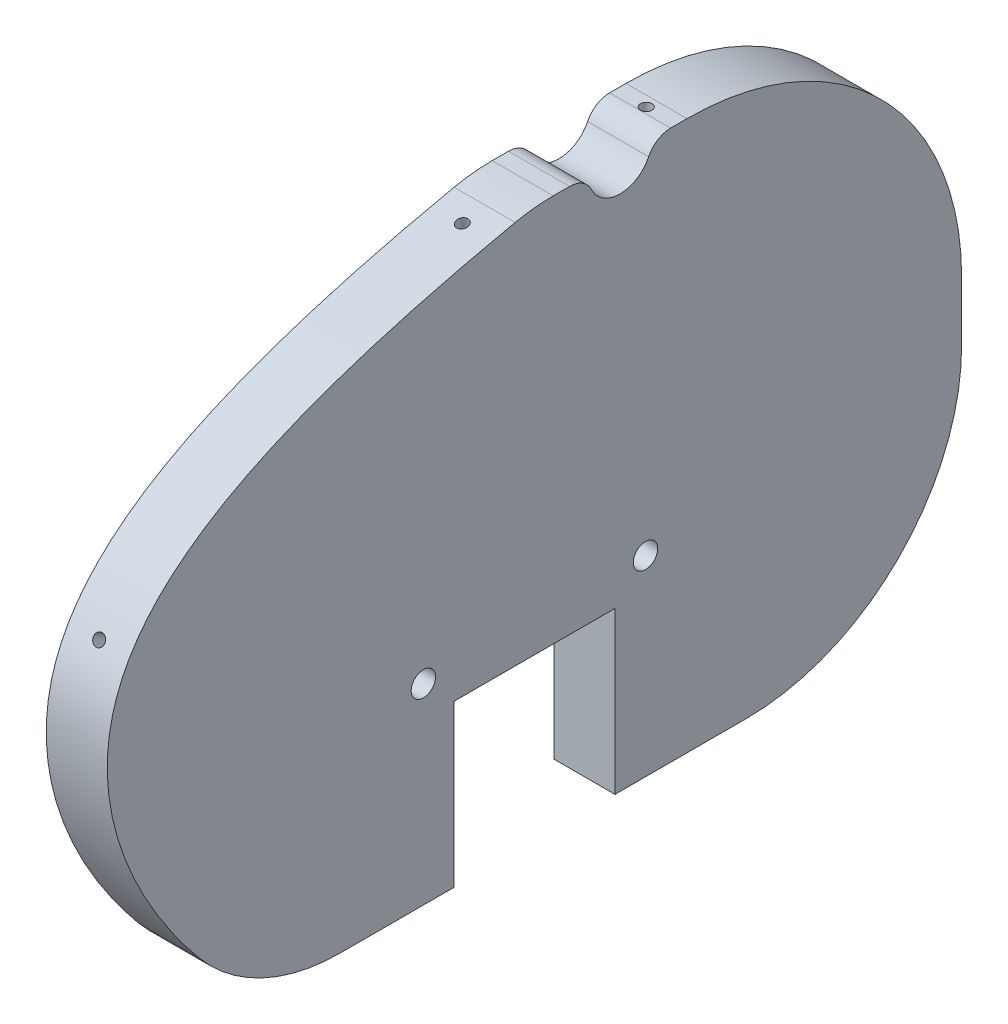
SolidWorks part; units mm, degrees
material "Oak"
ref_plane "Front Plane" through (0, 0, 0) normal (0, 0, 1) x (1, 0, 0)
ref_plane "Top Plane" through (0, 0, 0) normal (0, 1, 0) x (1, 0, 0)
ref_plane "Right Plane" through (0, 0, 0) normal (1, 0, 0) x (0, 0, -1)
sketch "Sketch1" plane through (0, 0, 0) normal (1, 0, 0) x (0, 0, -1)
  line L0 (0, 28.575) -> (0, -11.811) construction
  line L1 (1.949, 28.575) -> (15.875, 28.575)
  line L2 (-44.45, 0) -> (-44.45, -1.025)
  line L3 (-20.2212, -28.575) -> (-8.382, -28.575)
  line L4 (44.45, 0) -> (44.45, -6.1908)
  line L5 (-44.45, 28.575) -> (44.45, -28.575) construction
  line L6 (-44.45, -28.575) -> (44.45, 28.575) construction
  line L7 (-8.382, -11.811) -> (8.382, -11.811)
  line L8 (-8.382, -11.811) -> (-8.382, -28.575)
  line L9 (-44.45, 0) -> (0, 0) construction
  line L10 (8.382, -11.811) -> (8.382, -28.575)
  line L11 (-8.382, -11.811) -> (8.382, -28.575) construction
  line L12 (-8.382, -28.575) -> (8.382, -11.811) construction
  line L13 (8.382, -28.575) -> (22.0658, -28.575)
  line L14 (0, 0) -> (44.45, 0) construction
  arc A2 (22.0658, -28.575) -> (44.45, -6.1908) centre (22.0658, -6.1908) ccw
  arc A3 (44.45, 0) -> (15.875, 28.575) centre (15.875, 0) ccw
  arc A4 (-2.0065, 28.1598) -> (1.949, 28.575) centre (1.949, 9.525) cw
  arc A5 (-34.9185, -21.6448) -> (-20.2212, -28.575) centre (-20.2212, -9.525) ccw
  spline S0 degree 3 poles (-2.0065, 28.1598) (-30.4961, 22.1125) (-51.1965, 9.9804) (-41.1933, -14.0356) (-34.9185, -21.6448) knots 0.014283 0.014283 0.014283 0.014283 0.629768 0.915552 0.915552 0.915552 0.915552
  point P0 (0, 0)
  point P6 (0, -20.193)
  dimension "D5" = 19.05
  dimension "D6" = 19.05
  dimension "D1" = 88.9
  dimension "D2" = 57.15
  dimension "D3" = 16.764
  dimension "D4" = 16.764
extrude "Boss-Extrude1" add sketch "Sketch1" along normal mid plane 6.35 contours A4 S0 A5 L3 L8 L7 L10 L13 A2 L4 A3 L1
sketch "Sketch2" plane through (3.175, 0, 0) normal (1, 0, 0) x (0, 0, -1)
  line L0 (1.949, 28.575) -> (15.875, 28.575) construction
  circle A0 centre (8.912, 28.575) radius 3.302
  dimension "D1" = 6.604
extrude "Cut-Extrude1" cut sketch "Sketch2" against normal through all
fillet "Fillet1" radius 2.54 2 edges at (0, 28.575, -5.61) (0, 28.575, -12.214)
sketch "Sketch3" plane through (3.175, 0, 0) normal (1, 0, 0) x (0, 0, -1)
  line L0 (-8.382, -11.811) -> (8.382, -11.811) construction
  line L1 (8.382, -11.811) -> (8.382, -28.575) construction
  line L2 (-8.382, -11.811) -> (-8.382, -28.575) construction
  circle A0 centre (11.557, -8.636) radius 1.27
  circle A1 centre (-11.557, -8.636) radius 1.27
  dimension "D1" = 2.54
  dimension "D2" = 3.175
  dimension "D3" = 3.175
  dimension "D4" = 3.175
  dimension "D5" = 3.175
extrude "Cut-Extrude2" cut sketch "Sketch3" against normal through all
hole_wizard "3/64 (0.04688) Diameter Hole4" positions "3DSketch4" profile "Sketch7" hole size "3/64" standard "ANSI Inch"
sketch3d "3DSketch4"
  line L0 (3.175, 28.575, -1.949) -> (-3.175, 28.575, -1.949) construction
  point P0 (0, 27.6537, 4.3338)
  dimension "D1" = 6.35
sketch "Sketch7" plane through (0, 27.6537, 4.3338) normal (1, 0, 0) x (0, -0.2176, 0.976)
  line L0 (0, 0) -> (0, 6.7077)
  line L1 (0, 6.7077) -> (0.5954, 6.35)
  line L2 (0.5954, 6.35) -> (0.5954, 0)
  line L5 (0.5954, 0) -> (0, 0)
  line L10 (0, 6.7077) -> (-0.5954, 6.35) construction
  line L11 (0, -6.35) -> (0, 107.95) construction
  dimension "Hole Dia." = 1.1908
  dimension "Hole Depth" = 6.35
  dimension "Drill Angle" = 118
hole_wizard "3/64 (0.04688) Diameter Hole5" positions "Sketch9" profile "Sketch8" hole size "3/64" standard "ANSI Inch"
sketch "Sketch9" plane through (0, 28.575, 0) normal (0, 1, 0) x (1, 0, 0)
  line L0 (-3.175, 14.1729) -> (3.175, 14.1729) construction
  line L1 (0, -31.4325) -> (0, 31.4325) construction
  point P0 (0, 14.8079)
  dimension "D1" = 0.635
sketch "Sketch8" plane through (0, 28.575, -14.8079) normal (1, 0, 0) x (0, 0, 1)
  line L0 (0, 0) -> (0, 6.7077)
  line L1 (0, 6.7077) -> (0.5954, 6.35)
  line L2 (0.5954, 6.35) -> (0.5954, 0)
  line L5 (0.5954, 0) -> (0, 0)
  line L10 (0, 6.7077) -> (-0.5954, 6.35) construction
  line L11 (0, -6.35) -> (0, 107.95) construction
  dimension "Hole Dia." = 1.1908
  dimension "Hole Depth" = 6.35
  dimension "Drill Angle" = 118
hole_wizard "3/64 (0.04688) Diameter Hole8" positions "3DSketch7" profile "Sketch12" hole size "3/64" standard "ANSI Inch"
sketch3d "3DSketch7"
  line L0 (-3.175, -11.811, 8.382) -> (-3.175, -11.811, -8.382) construction
  point P0 (0, 6.9726, -43.5863)
  dimension "D1" = 19.05
sketch "Sketch12" plane through (0, 6.9726, -43.5863) normal (1, 0, 0) x (0, 0.9698, 0.244)
  line L0 (0, 0) -> (0, 6.7077)
  line L1 (0, 6.7077) -> (0.5954, 6.35)
  line L2 (0.5954, 6.35) -> (0.5954, 0)
  line L5 (0.5954, 0) -> (0, 0)
  line L10 (0, 6.7077) -> (-0.5954, 6.35) construction
  line L11 (0, -6.35) -> (0, 107.95) construction
  dimension "Hole Dia." = 1.1908
  dimension "Hole Depth" = 6.35
  dimension "Drill Angle" = 118
hole_wizard "3/64 (0.04688) Diameter Hole10" positions "3DSketch9" profile "Sketch14" hole size "3/64" standard "ANSI Inch"
sketch3d "3DSketch9"
  line L0 (3.175, -28.575, -22.0658) -> (-3.175, -28.575, -22.0658) construction
  point P0 (0, -20.4688, -39.305)
  dimension "D1" = 19.05
sketch "Sketch14" plane through (0, -20.4688, -39.305) normal (1, 0, 0) x (0, 0.7702, -0.6379)
  line L0 (0, 0) -> (0, 6.7077)
  line L1 (0, 6.7077) -> (0.5954, 6.35)
  line L2 (0.5954, 6.35) -> (0.5954, 0)
  line L5 (0.5954, 0) -> (0, 0)
  line L10 (0, 6.7077) -> (-0.5954, 6.35) construction
  line L11 (0, -6.35) -> (0, 107.95) construction
  dimension "Hole Dia." = 1.1908
  dimension "Hole Depth" = 6.35
  dimension "Drill Angle" = 118
hole_wizard "3/64 (0.04688) Diameter Hole11" positions "Sketch16" profile "Sketch15" hole size "3/64" standard "ANSI Inch"
sketch "Sketch16" plane through (0, -28.575, 0) normal (0, -1, 0) x (-1, 0, 0)
  line L0 (0, 31.4325) -> (0, -31.4325) construction
  line L1 (-3.175, 8.382) -> (3.175, 8.382) construction
  point P0 (0, 10.922)
  dimension "D1" = 2.54
sketch "Sketch15" plane through (0, -28.575, -10.922) normal (1, 0, 0) x (0, 0, -1)
  line L0 (0, 0) -> (0, 6.7077)
  line L1 (0, 6.7077) -> (0.5954, 6.35)
  line L2 (0.5954, 6.35) -> (0.5954, 0)
  line L5 (0.5954, 0) -> (0, 0)
  line L10 (0, 6.7077) -> (-0.5954, 6.35) construction
  line L11 (0, -6.35) -> (0, 107.95) construction
  dimension "Hole Dia." = 1.1908
  dimension "Hole Depth" = 6.35
  dimension "Drill Angle" = 118
hole_wizard "3/64 (0.04688) Diameter Hole12" positions "3DSketch10" profile "Sketch17" hole size "3/64" standard "ANSI Inch"
sketch3d "3DSketch10"
  line L0 (3.175, 28.1598, 2.0065) -> (-3.175, 28.1598, 2.0065) construction
  point P0 (0, 9.0162, 42.1229)
  dimension "D1" = 44.45
sketch "Sketch17" plane through (0, 9.0162, 42.1229) normal (1, 0, 0) x (0, -0.8625, 0.5061)
  line L0 (0, 0) -> (0, 6.7077)
  line L1 (0, 6.7077) -> (0.5954, 6.35)
  line L2 (0.5954, 6.35) -> (0.5954, 0)
  line L5 (0.5954, 0) -> (0, 0)
  line L10 (0, 6.7077) -> (-0.5954, 6.35) construction
  line L11 (0, -6.35) -> (0, 107.95) construction
  dimension "Hole Dia." = 1.1908
  dimension "Hole Depth" = 6.35
  dimension "Drill Angle" = 118
hole_wizard "3/64 (0.04688) Diameter Hole13" positions "3DSketch11" profile "Sketch18" hole size "3/64" standard "ANSI Inch"
sketch3d "3DSketch11"
  line L0 (3.175, -21.6448, 34.9185) -> (-3.175, -21.6448, 34.9185) construction
  point P0 (0, -25.8021, 30.1186)
  dimension "D1" = 6.35
sketch "Sketch18" plane through (0, -25.8021, 30.1186) normal (1, 0, 0) x (0, -0.5195, -0.8544)
  line L0 (0, 0) -> (0, 6.7077)
  line L1 (0, 6.7077) -> (0.5954, 6.35)
  line L2 (0.5954, 6.35) -> (0.5954, 0)
  line L5 (0.5954, 0) -> (0, 0)
  line L10 (0, 6.7077) -> (-0.5954, 6.35) construction
  line L11 (0, -6.35) -> (0, 107.95) construction
  dimension "Hole Dia." = 1.1908
  dimension "Hole Depth" = 6.35
  dimension "Drill Angle" = 118
hole_wizard "3/64 (0.04688) Diameter Hole14" positions "Sketch20" profile "Sketch19" hole size "3/64" standard "ANSI Inch"
sketch "Sketch20" plane through (0, -28.575, 0) normal (0, -1, 0) x (-1, 0, 0)
  line L0 (0, 31.4325) -> (0, -31.4325) construction
  line L1 (-3.175, -8.382) -> (3.175, -8.382) construction
  point P0 (0, -10.922)
  dimension "D1" = 2.54
sketch "Sketch19" plane through (0, -28.575, 10.922) normal (1, 0, 0) x (0, 0, -1)
  line L0 (0, 0) -> (0, 6.7077)
  line L1 (0, 6.7077) -> (0.5954, 6.35)
  line L2 (0.5954, 6.35) -> (0.5954, 0)
  line L5 (0.5954, 0) -> (0, 0)
  line L10 (0, 6.7077) -> (-0.5954, 6.35) construction
  line L11 (0, -6.35) -> (0, 107.95) construction
  dimension "Hole Dia." = 1.1908
  dimension "Hole Depth" = 6.35
  dimension "Drill Angle" = 118
